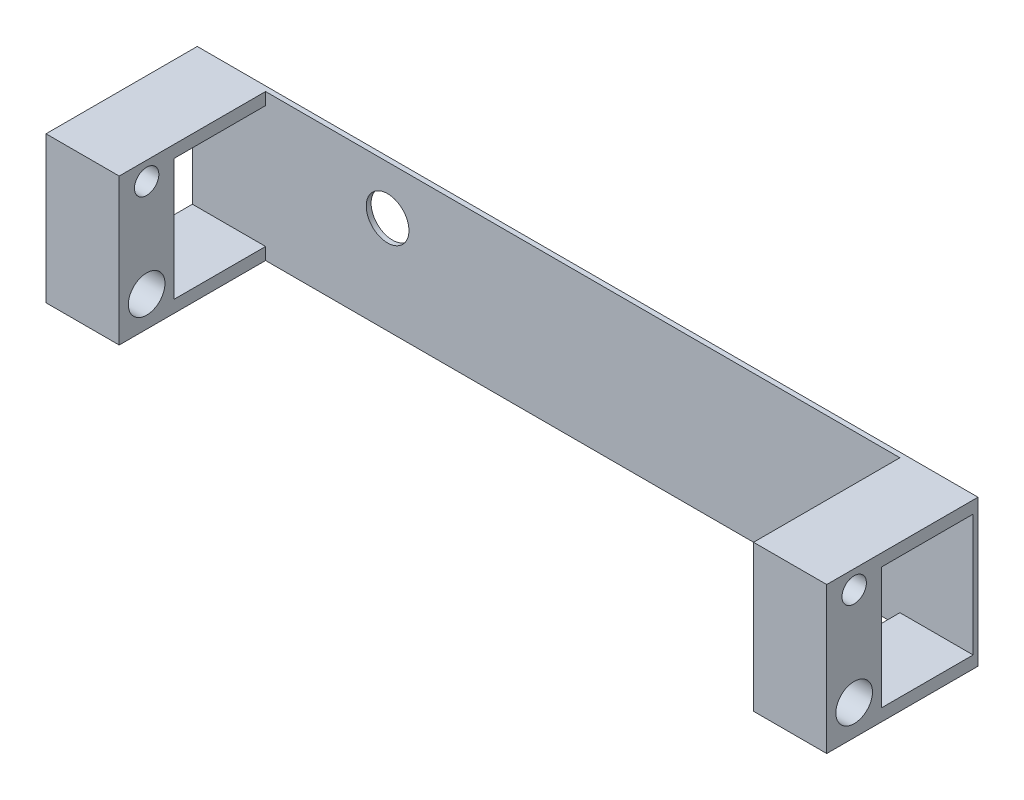
SolidWorks part; units mm, degrees
material "6061-T6 (SS)"
ref_plane "Front Plane" through (0, 0, 0) normal (0, 0, 1) x (1, 0, 0)
ref_plane "Top Plane" through (0, 0, 0) normal (0, 1, 0) x (1, 0, 0)
ref_plane "Right Plane" through (0, 0, 0) normal (1, 0, 0) x (0, 0, -1)
sketch "Sketch1" plane through (0, 0, 0) normal (0, 0, 1) x (1, 0, 0)
  line L0 (-152.4, 33.8131) -> (152.4, 33.8131) construction
  line L1 (-304.8, -16.9869) -> (304.8, -16.9869)
  line L2 (-304.8, -16.9869) -> (-304.8, 59.2131)
  line L3 (-304.8, 59.2131) -> (304.8, 59.2131)
  line L4 (304.8, -16.9869) -> (304.8, 59.2131)
  line L5 (0, 59.2131) -> (0, 33.8131) construction
  line L6 (0, 33.8131) -> (0, -16.9869) construction
  line L7 (0, 33.8131) -> (0, 142.4219) construction
  line L9 (0, 33.8131) -> (0, -74.7956) construction
  circle A0 centre (0, 33.8131) radius 11.1125
  point P11 (0, 33.8131)
  point P14 (0, 59.2131)
  dimension "D1" = 22.225
  dimension "D2" = 304.8
  dimension "D3" = 25.4
  dimension "D4" = 50.8
extrude "Boss-Extrude1" add sketch "Sketch1" along normal blind 2.54
sketch "Sketch2" plane through (0, 0, 2.54) normal (0, 0, 1) x (1, 0, 0)
  line L0 (-101.6, 59.2131) -> (-101.6, -16.9869) construction
  line L9 (-101.6, 59.2131) -> (-63.5, 59.2131)
  line L10 (-101.6, 59.2131) -> (-101.6, 52.8631)
  line L11 (-101.6, 52.8631) -> (-63.5, 52.8631)
  line L12 (-63.5, 59.2131) -> (-63.5, 52.8631)
  line L13 (-101.6, -16.9869) -> (-63.5, -16.9869)
  line L14 (-101.6, -16.9869) -> (-101.6, -10.6369)
  line L15 (-101.6, -10.6369) -> (-63.5, -10.6369)
  line L16 (-63.5, -16.9869) -> (-63.5, -10.6369)
  line L17 (304.8, 59.2131) -> (266.7, 59.2131)
  line L18 (304.8, 59.2131) -> (304.8, 52.8631)
  line L19 (304.8, 52.8631) -> (266.7, 52.8631)
  line L20 (266.7, 59.2131) -> (266.7, 52.8631)
  line L21 (304.8, -16.9869) -> (266.7, -16.9869)
  line L22 (304.8, -16.9869) -> (304.8, -10.6369)
  line L23 (304.8, -10.6369) -> (266.7, -10.6369)
  line L24 (266.7, -16.9869) -> (266.7, -10.6369)
  line L25 (-304.8, -16.9869) -> (304.8, -16.9869) construction
  line L26 (0, 33.8131) -> (0, 142.4219) construction
  point P3 (-63.5, 56.0381)
  dimension "D1" = 6.35
  dimension "D2" = 38.1
  dimension "D3" = 63.5
extrude "Boss-Extrude2" add sketch "Sketch2" along normal blind 76.2
sketch "Sketch3" plane through (0, 0, 78.74) normal (0, 0, 1) x (1, 0, 0)
  line L1 (-101.6, 59.2131) -> (-63.5, 59.2131)
  line L2 (-101.6, 59.2131) -> (-101.6, -16.9869)
  line L3 (-101.6, -16.9869) -> (-63.5, -16.9869)
  line L4 (-63.5, 59.2131) -> (-63.5, -16.9869)
  line L5 (266.7, 59.2131) -> (304.8, 59.2131)
  line L6 (266.7, 59.2131) -> (266.7, -16.9869)
  line L7 (266.7, -16.9869) -> (304.8, -16.9869)
  line L8 (304.8, 59.2131) -> (304.8, -16.9869)
extrude "Boss-Extrude3" add sketch "Sketch3" against normal blind 28.575
sketch "Sketch4" plane through (304.8, 0, 0) normal (1, 0, 0) x (0, 0, -1)
  line L0 (-50.165, 21.1131) -> (-78.74, 21.1131) construction
  line L1 (-50.165, -10.6369) -> (-50.165, 52.8631) construction
  line L2 (-78.74, -16.9869) -> (-78.74, 59.2131) construction
  line L3 (-64.4525, 49.6881) -> (-64.4525, -1.1119) construction
  circle A0 centre (-64.4525, 49.6881) radius 6.35
  circle A1 centre (-64.4525, -1.1119) radius 9.525
  point P11 (-64.4525, 21.1131)
  dimension "D1" = 19.05
  dimension "D2" = 28.575
  dimension ".5" = 12.7
  dimension "D3" = 22.225
extrude "Cut-Extrude1" cut sketch "Sketch4" against normal through all
sketch "Sketch5" plane through (0, 0, 2.54) normal (0, 0, 1) x (1, 0, 0)
  line L1 (-304.8, 59.2131) -> (-101.6, 59.2131)
  line L2 (-304.8, 59.2131) -> (-304.8, -16.9869)
  line L3 (-304.8, -16.9869) -> (-101.6, -16.9869)
  line L4 (-101.6, 59.2131) -> (-101.6, -16.9869)
extrude "Cut-Extrude2" cut sketch "Sketch5" against normal through all
